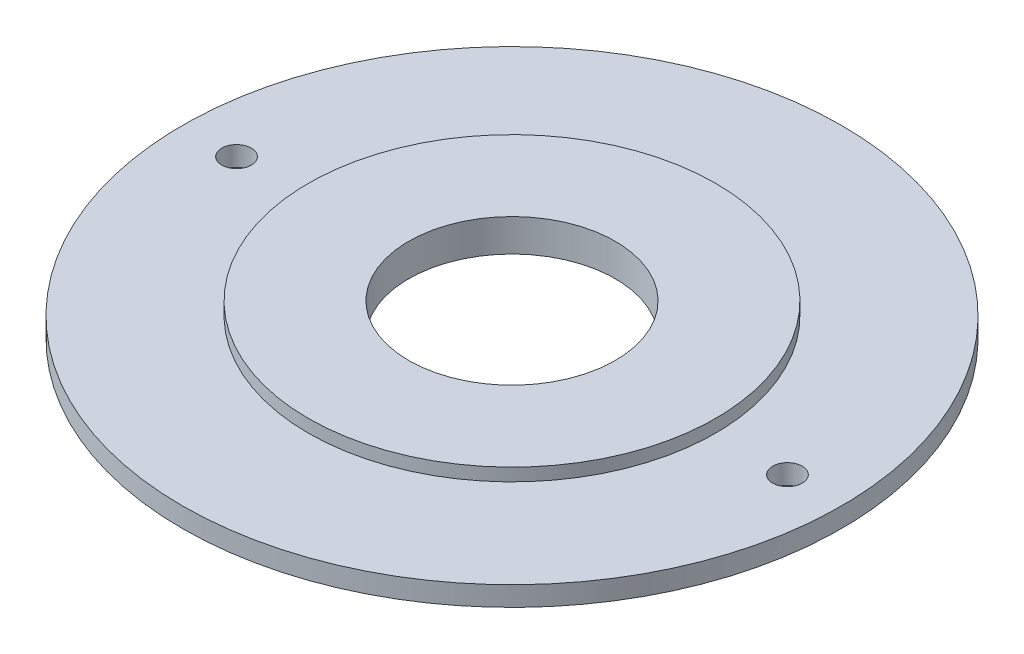
SolidWorks part; units mm, degrees
ref_plane "Спереди" through (0, 0, 0) normal (0, 0, 1) x (1, 0, 0)
ref_plane "Сверху" through (0, 0, 0) normal (0, 1, 0) x (1, 0, 0)
ref_plane "Справа" through (0, 0, 0) normal (1, 0, 0) x (0, 0, -1)
sketch "Эскиз1" plane through (0, 0, 0) normal (0, 1, 0) x (1, 0, 0)
  circle A0 centre (0, 0) radius 16.75
  dimension "D1" = 33.5
extrude "Бобышка-Вытянуть1" add sketch "Эскиз1" along normal blind 1
sketch "Эскиз2" plane through (0, 1, 0) normal (0, 1, 0) x (1, 0, 0)
  circle A0 centre (0, 0) radius 10.35
  dimension "D1" = 20.7
extrude "Бобышка-Вытянуть2" add sketch "Эскиз2" along normal blind 0.65
sketch "Эскиз3" plane through (0, 1.65, 0) normal (0, 1, 0) x (1, 0, 0)
  circle A0 centre (0, 0) radius 5.25
  dimension "D1" = 10.5
extrude "Вырез-Вытянуть1" cut sketch "Эскиз3" against normal through all
sketch "Эскиз4" plane through (0, 0, 0) normal (0, -1, 0) x (-1, 0, 0)
  circle A0 centre (-14, 0) radius 0.75
  circle A1 centre (14, 0) radius 0.75
  circle A2 centre (-14, 0) radius 0.75 construction
extrude "Вырез-Вытянуть2" cut sketch "Эскиз4" against normal through all
